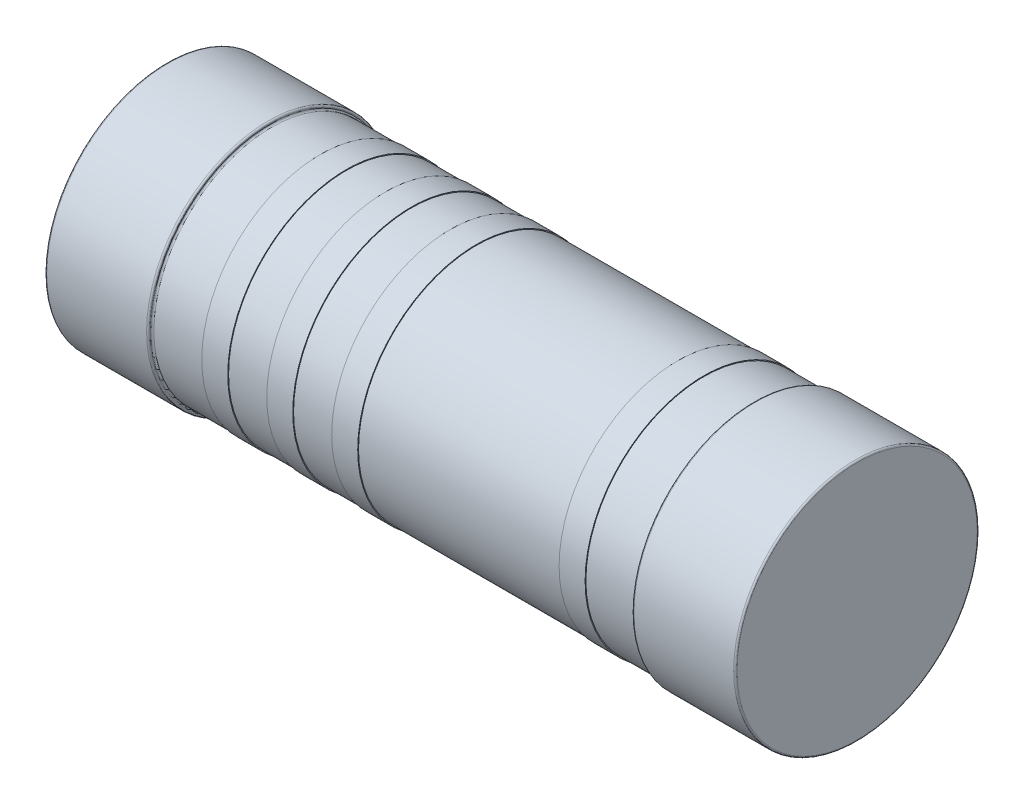
SolidWorks part; units mm, degrees
ref_plane "Front Plane" through (0, 0, 0) normal (0, 0, 1) x (1, 0, 0)
ref_plane "Top Plane" through (0, 0, 0) normal (0, 1, 0) x (1, 0, 0)
ref_plane "Right Plane" through (0, 0, 0) normal (1, 0, 0) x (0, 0, -1)
sketch "Sketch1" plane through (0, 0, 0) normal (0, 0, 1) x (1, 0, 0)
  line L0 (-4.25, 1.5) -> (4.25, 1.5)
  line L1 (0, 0) -> (0, 1.5) construction
  line L2 (-4.25, 1.5) -> (-3.0256, 1.5) construction
  line L3 (4.25, 1.5) -> (4.25, 0.02)
  line L4 (-4.23, 0) -> (-3, 0)
  line L5 (-4.25, 0.02) -> (-4.25, 1.5)
  line L6 (-2.98, 0.02) -> (-2.98, 0.03)
  line L7 (-2.96, 0.05) -> (-2.36, 0.05)
  line L8 (2.98, 0.03) -> (2.98, 0.02)
  line L9 (3, 0) -> (4.23, 0)
  line L10 (-2.36, 0.05) -> (-2.36, 0.04)
  line L11 (-2.36, 0.04) -> (-2.04, 0.04)
  line L12 (-2.04, 0.04) -> (-2.04, 0.05)
  line L13 (-1.56, 0.05) -> (-1.56, 0.04)
  line L14 (-1.56, 0.04) -> (-1.24, 0.04)
  line L15 (-1.24, 0.04) -> (-1.24, 0.05)
  line L16 (-0.44, 0.04) -> (-0.76, 0.04)
  line L17 (-0.76, 0.04) -> (-0.76, 0.05)
  line L18 (2.36, 0.05) -> (2.96, 0.05)
  line L19 (-0.44, 0.04) -> (-0.44, 0.05)
  line L20 (2.36, 0.05) -> (2.36, 0.04)
  line L21 (2.36, 0.04) -> (2.04, 0.04)
  line L22 (2.04, 0.04) -> (2.04, 0.05)
  line L23 (-2.2, 0.04) -> (-2.2, -0.0114) construction
  line L24 (-1.4, 0.04) -> (-1.4, -0.0114) construction
  line L25 (-0.6, 0.04) -> (-0.6, -0.0151) construction
  line L26 (2.2, 0.04) -> (2.2, -0.0151) construction
  line L27 (-0.44, 0.05) -> (2.04, 0.05)
  line L28 (-1.24, 0.05) -> (-0.76, 0.05)
  line L29 (-2.04, 0.05) -> (-1.56, 0.05)
  arc A0 (4.25, 0.02) -> (4.23, 0) centre (4.23, 0.02) cw
  arc A1 (3, 0) -> (2.98, 0.02) centre (3, 0.02) cw
  arc A2 (2.98, 0.03) -> (2.96, 0.05) centre (2.96, 0.03) ccw
  arc A3 (-2.96, 0.05) -> (-2.98, 0.03) centre (-2.96, 0.03) ccw
  arc A4 (-2.98, 0.02) -> (-3, 0) centre (-3, 0.02) cw
  arc A5 (-4.25, 0.02) -> (-4.23, 0) centre (-4.23, 0.02) ccw
  point P15 (4.25, 0)
  point P18 (2.98, 0)
  dimension "D5" = 0.02
  dimension "D1" = 8.5
  dimension "D2" = 1.27
  dimension "D3" = 0.05
  dimension "D4" = 1.5
  dimension "D6" = 0.32
  dimension "D7" = 0.01
  dimension "D8" = 0.8
  dimension "D9" = 0.8
  dimension "D10" = 0.6
  dimension "D11" = 2.2
revolve "Revolve1" add sketch "Sketch1" angle 360 about L2
